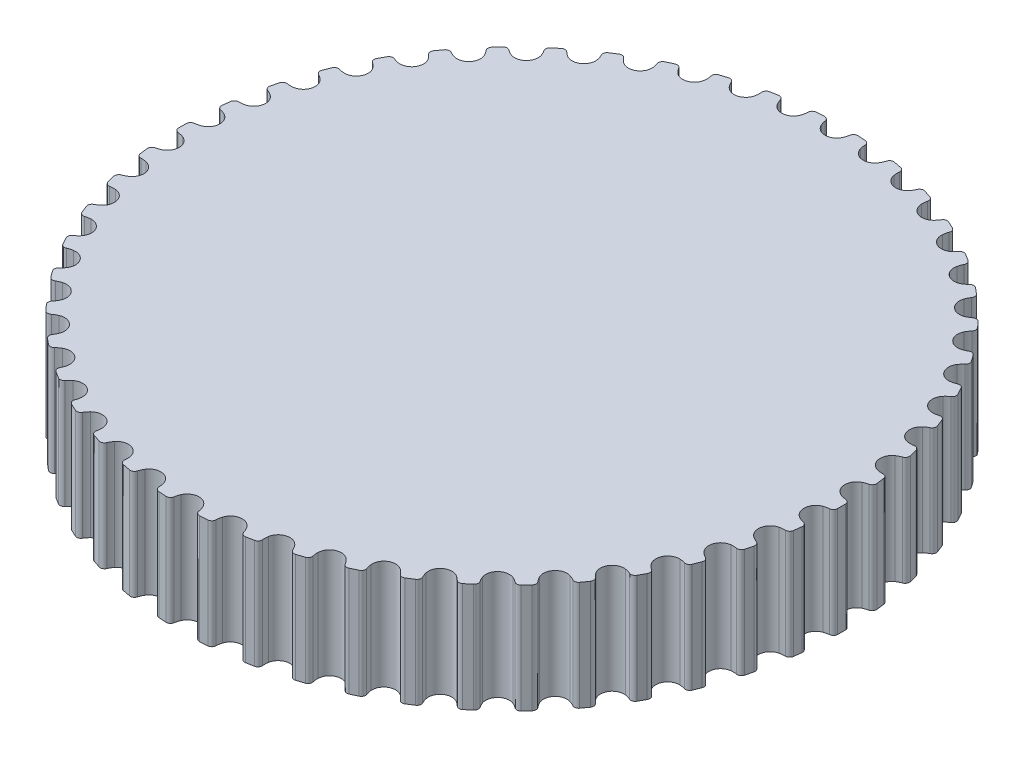
SolidWorks part; units mm, degrees
ref_plane "Front Plane" through (0, 0, 0) normal (0, 0, 1) x (1, 0, 0)
ref_plane "Top Plane" through (0, 0, 0) normal (0, 1, 0) x (1, 0, 0)
ref_plane "Right Plane" through (0, 0, 0) normal (1, 0, 0) x (0, 0, -1)
sketch "Sketch2" plane through (0, 0, 0) normal (0, 1, 0) x (1, 0, 0)
  line L0 (-2.9224, 39.1649) -> (-2.0093, 39.2223)
  line L1 (0, 0) -> (0, 24.0134) construction
  line L2 (-1.9774, 38.7153) -> (0, 38.7122) construction
  line L3 (1.9774, 38.7153) -> (0, 38.7122) construction
  line L4 (0, 0) -> (-2.9254, 23.2185) construction
  line L5 (2.0093, 39.2223) -> (2.9224, 39.1649)
  line L6 (6.9093, 38.6612) -> (7.8081, 38.4898)
  line L7 (11.7003, 37.4904) -> (12.5705, 37.2077)
  line L8 (16.3069, 35.7283) -> (17.1348, 35.3388)
  line L9 (20.6562, 33.4028) -> (21.4288, 32.9126)
  line L10 (24.6798, 30.5505) -> (25.3848, 29.9673)
  line L11 (28.3142, 27.2164) -> (28.9406, 26.5494)
  line L12 (31.5021, 23.4531) -> (32.0399, 22.7129)
  line L13 (34.1931, 19.3199) -> (34.6339, 18.5181)
  line L14 (36.3449, 14.882) -> (36.6818, 14.0313)
  line L15 (37.9236, 10.2094) -> (38.1511, 9.3232)
  line L16 (38.9041, 5.3759) -> (39.0188, 4.4681)
  line L17 (39.2711, 0.4575) -> (39.2711, -0.4575)
  line L18 (39.0188, -4.4681) -> (38.9041, -5.3759)
  line L19 (38.1511, -9.3232) -> (37.9236, -10.2094)
  line L20 (36.6818, -14.0313) -> (36.3449, -14.882)
  line L21 (34.6339, -18.5181) -> (34.1931, -19.3199)
  line L22 (32.0399, -22.7129) -> (31.5021, -23.4531)
  line L23 (28.9406, -26.5494) -> (28.3142, -27.2164)
  line L24 (25.3848, -29.9673) -> (24.6798, -30.5505)
  line L25 (21.4288, -32.9126) -> (20.6562, -33.4028)
  line L26 (17.1348, -35.3388) -> (16.3069, -35.7283)
  line L27 (12.5705, -37.2077) -> (11.7003, -37.4904)
  line L28 (7.8081, -38.4898) -> (6.9093, -38.6612)
  line L29 (2.9224, -39.1649) -> (2.0093, -39.2223)
  line L30 (-2.0093, -39.2223) -> (-2.9224, -39.1649)
  line L31 (-6.9093, -38.6612) -> (-7.8081, -38.4898)
  line L32 (-11.7003, -37.4904) -> (-12.5705, -37.2077)
  line L33 (-16.3069, -35.7283) -> (-17.1348, -35.3388)
  line L34 (-20.6562, -33.4028) -> (-21.4288, -32.9126)
  line L35 (-24.6798, -30.5505) -> (-25.3848, -29.9673)
  line L36 (-28.3142, -27.2164) -> (-28.9406, -26.5494)
  line L37 (-31.5021, -23.4531) -> (-32.0399, -22.7129)
  line L38 (-34.1931, -19.3199) -> (-34.6339, -18.5181)
  line L39 (-36.3449, -14.882) -> (-36.6818, -14.0313)
  line L40 (-37.9236, -10.2094) -> (-38.1511, -9.3232)
  line L41 (-38.9041, -5.3759) -> (-39.0188, -4.4681)
  line L42 (-39.2711, -0.4575) -> (-39.2711, 0.4575)
  line L43 (-39.0188, 4.4681) -> (-38.9041, 5.3759)
  line L44 (-38.1511, 9.3232) -> (-37.9236, 10.2094)
  line L45 (-36.6818, 14.0313) -> (-36.3449, 14.882)
  line L46 (-34.6339, 18.5181) -> (-34.1931, 19.3199)
  line L47 (-32.0399, 22.7129) -> (-31.5021, 23.4531)
  line L48 (-28.9406, 26.5494) -> (-28.3142, 27.2164)
  line L49 (-25.3848, 29.9673) -> (-24.6798, 30.5505)
  line L50 (-21.4288, 32.9126) -> (-20.6562, 33.4028)
  line L51 (-17.1348, 35.3388) -> (-16.3069, 35.7283)
  line L52 (-12.5705, 37.2077) -> (-11.7003, 37.4904)
  line L53 (-7.8081, 38.4898) -> (-6.9093, 38.6612)
  line L54 (0, 0) -> (1.2885, 38.153) construction
  arc A0 (-2.0093, 39.2223) -> (-1.4757, 38.7951) centre (-1.9774, 38.7153) cw
  arc A1 (-1.4757, 38.7951) -> (-1.2885, 38.153) centre (1.1557, 39.2137) ccw
  arc A2 (-1.2885, 38.153) -> (1.2885, 38.153) centre (0, 38.7122) ccw
  arc A3 (1.4757, 38.7951) -> (1.2885, 38.153) centre (-1.1557, 39.2137) cw
  arc A4 (2.0093, 39.2223) -> (1.4757, 38.7951) centre (1.9774, 38.7153) ccw
  arc A5 (0, 38.7122) -> (-4.8393, 38.4085) centre (0, 0) ccw construction
  arc A6 (2.9224, 39.1649) -> (3.3983, 38.6742) centre (2.8905, 38.6579) cw
  arc A7 (3.3983, 38.6742) -> (3.5035, 38.0136) centre (6.0614, 38.7596) ccw
  arc A8 (3.5035, 38.0136) -> (6.0602, 37.6906) centre (4.8519, 38.4069) ccw
  arc A9 (6.3264, 38.3043) -> (6.0602, 37.6906) centre (3.7682, 39.0493) cw
  arc A10 (6.9093, 38.6612) -> (6.3264, 38.3043) centre (6.8141, 38.1622) ccw
  arc A11 (7.8081, 38.4898) -> (8.2186, 37.9433) centre (7.7129, 37.9908) cw
  arc A12 (8.2186, 37.9433) -> (8.2402, 37.2748) centre (10.8714, 37.6943) ccw
  arc A13 (8.2402, 37.2748) -> (10.7363, 36.6339) centre (9.6273, 37.4959) ccw
  arc A14 (11.0773, 37.2093) -> (10.7363, 36.6339) centre (8.6327, 38.2691) cw
  arc A15 (11.7003, 37.4904) -> (11.0773, 37.2093) centre (11.5434, 37.0073) ccw
  arc A16 (12.5705, 37.2077) -> (12.9094, 36.614) centre (12.4136, 36.7245) cw
  arc A17 (12.9094, 36.614) -> (12.847, 35.9481) centre (15.5101, 36.0345) ccw
  arc A18 (12.847, 35.9481) -> (15.2431, 34.9994) centre (14.2509, 35.9937) ccw
  arc A19 (15.6535, 35.5276) -> (15.2431, 34.9994) centre (13.361, 36.8854) cw
  arc A20 (16.3069, 35.7283) -> (15.6535, 35.5276) centre (16.0906, 35.2687) ccw
  arc A21 (17.1348, 35.3388) -> (17.3966, 34.7074) centre (16.9185, 34.8791) cw
  arc A22 (17.3966, 34.7074) -> (17.2512, 34.0544) centre (19.9041, 33.8065) ccw
  arc A23 (17.2512, 34.0544) -> (19.5095, 32.813) centre (18.6497, 33.9237) ccw
  arc A24 (19.9828, 33.2855) -> (19.5095, 32.813) centre (17.8786, 34.92) cw
  arc A25 (20.6562, 33.4028) -> (19.9828, 33.2855) centre (20.384, 32.9739) ccw
  arc A26 (21.4288, 32.9126) -> (21.6094, 32.2533) centre (21.1566, 32.4836) cw
  arc A27 (21.6094, 32.2533) -> (21.3833, 31.6238) centre (23.9842, 31.0453) ccw
  arc A28 (21.3833, 31.6238) -> (23.4682, 30.109) centre (22.7544, 31.3188) ccw
  arc A29 (23.9971, 30.5185) -> (23.4682, 30.109) centre (22.1143, 32.4039) cw
  arc A30 (24.6798, 30.5505) -> (23.9971, 30.5185) centre (24.356, 30.1591) ccw
  arc A31 (25.3848, 29.9673) -> (25.4814, 29.2906) centre (25.061, 29.5759) cw
  arc A32 (25.4814, 29.2906) -> (25.1782, 28.6944) centre (27.6861, 27.7944) ccw
  arc A33 (25.1782, 28.6944) -> (27.0568, 26.9303) centre (26.5003, 28.2199) ccw
  arc A34 (27.6328, 27.2703) -> (27.0568, 26.9303) centre (26.0012, 29.3767) cw
  arc A35 (28.3142, 27.2164) -> (27.6328, 27.2703) centre (27.9439, 26.8687) ccw
  arc A36 (28.9406, 26.5494) -> (28.9515, 25.866) centre (28.5703, 26.2017) cw
  arc A37 (28.9515, 25.866) -> (28.576, 25.3124) centre (30.9514, 24.1053) ccw
  arc A38 (28.576, 25.3124) -> (30.2187, 23.3268) centre (29.8282, 24.6761) ccw
  arc A39 (30.8328, 23.5919) -> (30.2187, 23.3268) centre (29.478, 25.8862) cw
  arc A40 (31.5021, 23.4531) -> (30.8328, 23.5919) centre (31.0911, 23.1545) ccw
  arc A41 (32.0399, 22.7129) -> (31.9651, 22.0334) centre (31.6289, 22.4143) cw
  arc A42 (31.9651, 22.0334) -> (31.5232, 21.5313) centre (33.7285, 20.036) ccw
  arc A43 (31.5232, 21.5313) -> (32.904, 19.3555) centre (32.6858, 20.743) ccw
  arc A44 (33.5465, 19.5415) -> (32.904, 19.3555) centre (32.49, 21.9875) cw
  arc A45 (34.1931, 19.3199) -> (33.5465, 19.5415) centre (33.748, 19.0752) ccw
  arc A46 (34.6339, 18.5181) -> (34.4746, 17.8534) centre (34.1888, 18.2734) cw
  arc A47 (34.4746, 17.8534) -> (33.9732, 17.4106) centre (35.9737, 15.6507) ccw
  arc A48 (33.9732, 17.4106) -> (35.0705, 15.0789) centre (35.0278, 16.4828) ccw
  arc A49 (35.7312, 15.1829) -> (35.0705, 15.0789) centre (34.9896, 17.7421) cw
  arc A50 (36.3449, 14.882) -> (35.7312, 15.1829) centre (35.8726, 14.695) ccw
  arc A51 (36.6818, 14.0313) -> (36.4404, 13.3918) centre (36.2094, 13.8443) cw
  arc A52 (36.4404, 13.3918) -> (35.8875, 13.0154) centre (37.6516, 11.0186) ccw
  arc A53 (35.8875, 13.0154) -> (36.6838, 10.5645) centre (36.8174, 11.9627) ccw
  arc A54 (37.3524, 10.5849) -> (36.6838, 10.5645) centre (36.9373, 13.2168) cw
  arc A55 (37.9236, 10.2094) -> (37.3524, 10.5849) centre (37.4315, 10.0831) ccw
  arc A56 (38.1511, 9.3232) -> (37.8315, 8.719) centre (37.6591, 9.1969) cw
  arc A57 (37.8315, 8.719) -> (37.2357, 8.4148) centre (38.7357, 6.2127) ccw
  arc A58 (37.2357, 8.4148) -> (37.7186, 5.8835) centre (38.0265, 7.2539) ccw
  arc A59 (38.3845, 5.8199) -> (37.7186, 5.8835) centre (38.3026, 8.4831) cw
  arc A60 (38.9041, 5.3759) -> (38.3845, 5.8199) centre (38.4001, 5.3122) ccw
  arc A61 (39.0188, 4.4681) -> (38.6259, 3.9087) centre (38.5148, 4.4044) cw
  arc A62 (38.6259, 3.9087) -> (37.9968, 3.6816) centre (39.2089, 1.3088) ccw
  arc A63 (37.9968, 3.6816) -> (38.1586, 1.1097) centre (38.6358, 2.4308) ccw
  arc A64 (38.8112, 0.9632) -> (38.1586, 1.1097) centre (39.0638, 3.6157) cw
  arc A65 (39.2711, 0.4575) -> (38.8112, 0.9632) centre (38.7631, 0.4575) ccw
  arc A66 (39.2711, -0.4575) -> (38.8112, -0.9632) centre (38.7631, -0.4575) cw
  arc A67 (38.8112, -0.9632) -> (38.1586, -1.1097) centre (39.0638, -3.6157) ccw
  arc A68 (38.1586, -1.1097) -> (37.9968, -3.6816) centre (38.6358, -2.4308) ccw
  arc A69 (38.6259, -3.9087) -> (37.9968, -3.6816) centre (39.2089, -1.3088) cw
  arc A70 (39.0188, -4.4681) -> (38.6259, -3.9087) centre (38.5148, -4.4044) ccw
  arc A71 (38.9041, -5.3759) -> (38.3845, -5.8199) centre (38.4001, -5.3122) cw
  arc A72 (38.3845, -5.8199) -> (37.7186, -5.8835) centre (38.3026, -8.4831) ccw
  arc A73 (37.7186, -5.8835) -> (37.2357, -8.4148) centre (38.0265, -7.2539) ccw
  arc A74 (37.8315, -8.719) -> (37.2357, -8.4148) centre (38.7357, -6.2127) cw
  arc A75 (38.1511, -9.3232) -> (37.8315, -8.719) centre (37.6591, -9.1969) ccw
  arc A76 (37.9236, -10.2094) -> (37.3524, -10.5849) centre (37.4315, -10.0831) cw
  arc A77 (37.3524, -10.5849) -> (36.6838, -10.5645) centre (36.9373, -13.2168) ccw
  arc A78 (36.6838, -10.5645) -> (35.8875, -13.0154) centre (36.8174, -11.9627) ccw
  arc A79 (36.4404, -13.3918) -> (35.8875, -13.0154) centre (37.6516, -11.0186) cw
  arc A80 (36.6818, -14.0313) -> (36.4404, -13.3918) centre (36.2094, -13.8443) ccw
  arc A81 (36.3449, -14.882) -> (35.7312, -15.1829) centre (35.8726, -14.695) cw
  arc A82 (35.7312, -15.1829) -> (35.0705, -15.0789) centre (34.9896, -17.7421) ccw
  arc A83 (35.0705, -15.0789) -> (33.9732, -17.4106) centre (35.0278, -16.4828) ccw
  arc A84 (34.4746, -17.8534) -> (33.9732, -17.4106) centre (35.9737, -15.6507) cw
  arc A85 (34.6339, -18.5181) -> (34.4746, -17.8534) centre (34.1888, -18.2734) ccw
  arc A86 (34.1931, -19.3199) -> (33.5465, -19.5415) centre (33.748, -19.0752) cw
  arc A87 (33.5465, -19.5415) -> (32.904, -19.3555) centre (32.49, -21.9875) ccw
  arc A88 (32.904, -19.3555) -> (31.5232, -21.5313) centre (32.6858, -20.743) ccw
  arc A89 (31.9651, -22.0334) -> (31.5232, -21.5313) centre (33.7285, -20.036) cw
  arc A90 (32.0399, -22.7129) -> (31.9651, -22.0334) centre (31.6289, -22.4143) ccw
  arc A91 (31.5021, -23.4531) -> (30.8328, -23.5919) centre (31.0911, -23.1545) cw
  arc A92 (30.8328, -23.5919) -> (30.2187, -23.3268) centre (29.478, -25.8862) ccw
  arc A93 (30.2187, -23.3268) -> (28.576, -25.3124) centre (29.8282, -24.6761) ccw
  arc A94 (28.9515, -25.866) -> (28.576, -25.3124) centre (30.9514, -24.1053) cw
  arc A95 (28.9406, -26.5494) -> (28.9515, -25.866) centre (28.5703, -26.2017) ccw
  arc A96 (28.3142, -27.2164) -> (27.6328, -27.2703) centre (27.9439, -26.8687) cw
  arc A97 (27.6328, -27.2703) -> (27.0568, -26.9303) centre (26.0012, -29.3767) ccw
  arc A98 (27.0568, -26.9303) -> (25.1782, -28.6944) centre (26.5003, -28.2199) ccw
  arc A99 (25.4814, -29.2906) -> (25.1782, -28.6944) centre (27.6861, -27.7944) cw
  arc A100 (25.3848, -29.9673) -> (25.4814, -29.2906) centre (25.061, -29.5759) ccw
  arc A101 (24.6798, -30.5505) -> (23.9971, -30.5185) centre (24.356, -30.1591) cw
  arc A102 (23.9971, -30.5185) -> (23.4682, -30.109) centre (22.1143, -32.4039) ccw
  arc A103 (23.4682, -30.109) -> (21.3833, -31.6238) centre (22.7544, -31.3188) ccw
  arc A104 (21.6094, -32.2533) -> (21.3833, -31.6238) centre (23.9842, -31.0453) cw
  arc A105 (21.4288, -32.9126) -> (21.6094, -32.2533) centre (21.1566, -32.4836) ccw
  arc A106 (20.6562, -33.4028) -> (19.9828, -33.2855) centre (20.384, -32.9739) cw
  arc A107 (19.9828, -33.2855) -> (19.5095, -32.813) centre (17.8786, -34.92) ccw
  arc A108 (19.5095, -32.813) -> (17.2512, -34.0544) centre (18.6497, -33.9237) ccw
  arc A109 (17.3966, -34.7074) -> (17.2512, -34.0544) centre (19.9041, -33.8065) cw
  arc A110 (17.1348, -35.3388) -> (17.3966, -34.7074) centre (16.9185, -34.8791) ccw
  arc A111 (16.3069, -35.7283) -> (15.6535, -35.5276) centre (16.0906, -35.2687) cw
  arc A112 (15.6535, -35.5276) -> (15.2431, -34.9994) centre (13.361, -36.8854) ccw
  arc A113 (15.2431, -34.9994) -> (12.847, -35.9481) centre (14.2509, -35.9937) ccw
  arc A114 (12.9094, -36.614) -> (12.847, -35.9481) centre (15.5101, -36.0345) cw
  arc A115 (12.5705, -37.2077) -> (12.9094, -36.614) centre (12.4136, -36.7245) ccw
  arc A116 (11.7003, -37.4904) -> (11.0773, -37.2093) centre (11.5434, -37.0073) cw
  arc A117 (11.0773, -37.2093) -> (10.7363, -36.6339) centre (8.6327, -38.2691) ccw
  arc A118 (10.7363, -36.6339) -> (8.2402, -37.2748) centre (9.6273, -37.4959) ccw
  arc A119 (8.2186, -37.9433) -> (8.2402, -37.2748) centre (10.8714, -37.6943) cw
  arc A120 (7.8081, -38.4898) -> (8.2186, -37.9433) centre (7.7129, -37.9908) ccw
  arc A121 (6.9093, -38.6612) -> (6.3264, -38.3043) centre (6.8141, -38.1622) cw
  arc A122 (6.3264, -38.3043) -> (6.0602, -37.6906) centre (3.7682, -39.0493) ccw
  arc A123 (6.0602, -37.6906) -> (3.5035, -38.0136) centre (4.8519, -38.4069) ccw
  arc A124 (3.3983, -38.6742) -> (3.5035, -38.0136) centre (6.0614, -38.7596) cw
  arc A125 (2.9224, -39.1649) -> (3.3983, -38.6742) centre (2.8905, -38.6579) ccw
  arc A126 (2.0093, -39.2223) -> (1.4757, -38.7951) centre (1.9774, -38.7153) cw
  arc A127 (1.4757, -38.7951) -> (1.2885, -38.153) centre (-1.1557, -39.2137) ccw
  arc A128 (1.2885, -38.153) -> (-1.2885, -38.153) centre (0, -38.7122) ccw
  arc A129 (-1.4757, -38.7951) -> (-1.2885, -38.153) centre (1.1557, -39.2137) cw
  arc A130 (-2.0093, -39.2223) -> (-1.4757, -38.7951) centre (-1.9774, -38.7153) ccw
  arc A131 (-2.9224, -39.1649) -> (-3.3983, -38.6742) centre (-2.8905, -38.6579) cw
  arc A132 (-3.3983, -38.6742) -> (-3.5035, -38.0136) centre (-6.0614, -38.7596) ccw
  arc A133 (-3.5035, -38.0136) -> (-6.0602, -37.6906) centre (-4.8519, -38.4069) ccw
  arc A134 (-6.3264, -38.3043) -> (-6.0602, -37.6906) centre (-3.7682, -39.0493) cw
  arc A135 (-6.9093, -38.6612) -> (-6.3264, -38.3043) centre (-6.8141, -38.1622) ccw
  arc A136 (-7.8081, -38.4898) -> (-8.2186, -37.9433) centre (-7.7129, -37.9908) cw
  arc A137 (-8.2186, -37.9433) -> (-8.2402, -37.2748) centre (-10.8714, -37.6943) ccw
  arc A138 (-8.2402, -37.2748) -> (-10.7363, -36.6339) centre (-9.6273, -37.4959) ccw
  arc A139 (-11.0773, -37.2093) -> (-10.7363, -36.6339) centre (-8.6327, -38.2691) cw
  arc A140 (-11.7003, -37.4904) -> (-11.0773, -37.2093) centre (-11.5434, -37.0073) ccw
  arc A141 (-12.5705, -37.2077) -> (-12.9094, -36.614) centre (-12.4136, -36.7245) cw
  arc A142 (-12.9094, -36.614) -> (-12.847, -35.9481) centre (-15.5101, -36.0345) ccw
  arc A143 (-12.847, -35.9481) -> (-15.2431, -34.9994) centre (-14.2509, -35.9937) ccw
  arc A144 (-15.6535, -35.5276) -> (-15.2431, -34.9994) centre (-13.361, -36.8854) cw
  arc A145 (-16.3069, -35.7283) -> (-15.6535, -35.5276) centre (-16.0906, -35.2687) ccw
  arc A146 (-17.1348, -35.3388) -> (-17.3966, -34.7074) centre (-16.9185, -34.8791) cw
  arc A147 (-17.3966, -34.7074) -> (-17.2512, -34.0544) centre (-19.9041, -33.8065) ccw
  arc A148 (-17.2512, -34.0544) -> (-19.5095, -32.813) centre (-18.6497, -33.9237) ccw
  arc A149 (-19.9828, -33.2855) -> (-19.5095, -32.813) centre (-17.8786, -34.92) cw
  arc A150 (-20.6562, -33.4028) -> (-19.9828, -33.2855) centre (-20.384, -32.9739) ccw
  arc A151 (-21.4288, -32.9126) -> (-21.6094, -32.2533) centre (-21.1566, -32.4836) cw
  arc A152 (-21.6094, -32.2533) -> (-21.3833, -31.6238) centre (-23.9842, -31.0453) ccw
  arc A153 (-21.3833, -31.6238) -> (-23.4682, -30.109) centre (-22.7544, -31.3188) ccw
  arc A154 (-23.9971, -30.5185) -> (-23.4682, -30.109) centre (-22.1143, -32.4039) cw
  arc A155 (-24.6798, -30.5505) -> (-23.9971, -30.5185) centre (-24.356, -30.1591) ccw
  arc A156 (-25.3848, -29.9673) -> (-25.4814, -29.2906) centre (-25.061, -29.5759) cw
  arc A157 (-25.4814, -29.2906) -> (-25.1782, -28.6944) centre (-27.6861, -27.7944) ccw
  arc A158 (-25.1782, -28.6944) -> (-27.0568, -26.9303) centre (-26.5003, -28.2199) ccw
  arc A159 (-27.6328, -27.2703) -> (-27.0568, -26.9303) centre (-26.0012, -29.3767) cw
  arc A160 (-28.3142, -27.2164) -> (-27.6328, -27.2703) centre (-27.9439, -26.8687) ccw
  arc A161 (-28.9406, -26.5494) -> (-28.9515, -25.866) centre (-28.5703, -26.2017) cw
  arc A162 (-28.9515, -25.866) -> (-28.576, -25.3124) centre (-30.9514, -24.1053) ccw
  arc A163 (-28.576, -25.3124) -> (-30.2187, -23.3268) centre (-29.8282, -24.6761) ccw
  arc A164 (-30.8328, -23.5919) -> (-30.2187, -23.3268) centre (-29.478, -25.8862) cw
  arc A165 (-31.5021, -23.4531) -> (-30.8328, -23.5919) centre (-31.0911, -23.1545) ccw
  arc A166 (-32.0399, -22.7129) -> (-31.9651, -22.0334) centre (-31.6289, -22.4143) cw
  arc A167 (-31.9651, -22.0334) -> (-31.5232, -21.5313) centre (-33.7285, -20.036) ccw
  arc A168 (-31.5232, -21.5313) -> (-32.904, -19.3555) centre (-32.6858, -20.743) ccw
  arc A169 (-33.5465, -19.5415) -> (-32.904, -19.3555) centre (-32.49, -21.9875) cw
  arc A170 (-34.1931, -19.3199) -> (-33.5465, -19.5415) centre (-33.748, -19.0752) ccw
  arc A171 (-34.6339, -18.5181) -> (-34.4746, -17.8534) centre (-34.1888, -18.2734) cw
  arc A172 (-34.4746, -17.8534) -> (-33.9732, -17.4106) centre (-35.9737, -15.6507) ccw
  arc A173 (-33.9732, -17.4106) -> (-35.0705, -15.0789) centre (-35.0278, -16.4828) ccw
  arc A174 (-35.7312, -15.1829) -> (-35.0705, -15.0789) centre (-34.9896, -17.7421) cw
  arc A175 (-36.3449, -14.882) -> (-35.7312, -15.1829) centre (-35.8726, -14.695) ccw
  arc A176 (-36.6818, -14.0313) -> (-36.4404, -13.3918) centre (-36.2094, -13.8443) cw
  arc A177 (-36.4404, -13.3918) -> (-35.8875, -13.0154) centre (-37.6516, -11.0186) ccw
  arc A178 (-35.8875, -13.0154) -> (-36.6838, -10.5645) centre (-36.8174, -11.9627) ccw
  arc A179 (-37.3524, -10.5849) -> (-36.6838, -10.5645) centre (-36.9373, -13.2168) cw
  arc A180 (-37.9236, -10.2094) -> (-37.3524, -10.5849) centre (-37.4315, -10.0831) ccw
  arc A181 (-38.1511, -9.3232) -> (-37.8315, -8.719) centre (-37.6591, -9.1969) cw
  arc A182 (-37.8315, -8.719) -> (-37.2357, -8.4148) centre (-38.7357, -6.2127) ccw
  arc A183 (-37.2357, -8.4148) -> (-37.7186, -5.8835) centre (-38.0265, -7.2539) ccw
  arc A184 (-38.3845, -5.8199) -> (-37.7186, -5.8835) centre (-38.3026, -8.4831) cw
  arc A185 (-38.9041, -5.3759) -> (-38.3845, -5.8199) centre (-38.4001, -5.3122) ccw
  arc A186 (-39.0188, -4.4681) -> (-38.6259, -3.9087) centre (-38.5148, -4.4044) cw
  arc A187 (-38.6259, -3.9087) -> (-37.9968, -3.6816) centre (-39.2089, -1.3088) ccw
  arc A188 (-37.9968, -3.6816) -> (-38.1586, -1.1097) centre (-38.6358, -2.4308) ccw
  arc A189 (-38.8112, -0.9632) -> (-38.1586, -1.1097) centre (-39.0638, -3.6157) cw
  arc A190 (-39.2711, -0.4575) -> (-38.8112, -0.9632) centre (-38.7631, -0.4575) ccw
  arc A191 (-39.2711, 0.4575) -> (-38.8112, 0.9632) centre (-38.7631, 0.4575) cw
  arc A192 (-38.8112, 0.9632) -> (-38.1586, 1.1097) centre (-39.0638, 3.6157) ccw
  arc A193 (-38.1586, 1.1097) -> (-37.9968, 3.6816) centre (-38.6358, 2.4308) ccw
  arc A194 (-38.6259, 3.9087) -> (-37.9968, 3.6816) centre (-39.2089, 1.3088) cw
  arc A195 (-39.0188, 4.4681) -> (-38.6259, 3.9087) centre (-38.5148, 4.4044) ccw
  arc A196 (-38.9041, 5.3759) -> (-38.3845, 5.8199) centre (-38.4001, 5.3122) cw
  arc A197 (-38.3845, 5.8199) -> (-37.7186, 5.8835) centre (-38.3026, 8.4831) ccw
  arc A198 (-37.7186, 5.8835) -> (-37.2357, 8.4148) centre (-38.0265, 7.2539) ccw
  arc A199 (-37.8315, 8.719) -> (-37.2357, 8.4148) centre (-38.7357, 6.2127) cw
  arc A200 (-38.1511, 9.3232) -> (-37.8315, 8.719) centre (-37.6591, 9.1969) ccw
  arc A201 (-37.9236, 10.2094) -> (-37.3524, 10.5849) centre (-37.4315, 10.0831) cw
  arc A202 (-37.3524, 10.5849) -> (-36.6838, 10.5645) centre (-36.9373, 13.2168) ccw
  arc A203 (-36.6838, 10.5645) -> (-35.8875, 13.0154) centre (-36.8174, 11.9627) ccw
  arc A204 (-36.4404, 13.3918) -> (-35.8875, 13.0154) centre (-37.6516, 11.0186) cw
  arc A205 (-36.6818, 14.0313) -> (-36.4404, 13.3918) centre (-36.2094, 13.8443) ccw
  arc A206 (-36.3449, 14.882) -> (-35.7312, 15.1829) centre (-35.8726, 14.695) cw
  arc A207 (-35.7312, 15.1829) -> (-35.0705, 15.0789) centre (-34.9896, 17.7421) ccw
  arc A208 (-35.0705, 15.0789) -> (-33.9732, 17.4106) centre (-35.0278, 16.4828) ccw
  arc A209 (-34.4746, 17.8534) -> (-33.9732, 17.4106) centre (-35.9737, 15.6507) cw
  arc A210 (-34.6339, 18.5181) -> (-34.4746, 17.8534) centre (-34.1888, 18.2734) ccw
  arc A211 (-34.1931, 19.3199) -> (-33.5465, 19.5415) centre (-33.748, 19.0752) cw
  arc A212 (-33.5465, 19.5415) -> (-32.904, 19.3555) centre (-32.49, 21.9875) ccw
  arc A213 (-32.904, 19.3555) -> (-31.5232, 21.5313) centre (-32.6858, 20.743) ccw
  arc A214 (-31.9651, 22.0334) -> (-31.5232, 21.5313) centre (-33.7285, 20.036) cw
  arc A215 (-32.0399, 22.7129) -> (-31.9651, 22.0334) centre (-31.6289, 22.4143) ccw
  arc A216 (-31.5021, 23.4531) -> (-30.8328, 23.5919) centre (-31.0911, 23.1545) cw
  arc A217 (-30.8328, 23.5919) -> (-30.2187, 23.3268) centre (-29.478, 25.8862) ccw
  arc A218 (-30.2187, 23.3268) -> (-28.576, 25.3124) centre (-29.8282, 24.6761) ccw
  arc A219 (-28.9515, 25.866) -> (-28.576, 25.3124) centre (-30.9514, 24.1053) cw
  arc A220 (-28.9406, 26.5494) -> (-28.9515, 25.866) centre (-28.5703, 26.2017) ccw
  arc A221 (-28.3142, 27.2164) -> (-27.6328, 27.2703) centre (-27.9439, 26.8687) cw
  arc A222 (-27.6328, 27.2703) -> (-27.0568, 26.9303) centre (-26.0012, 29.3767) ccw
  arc A223 (-27.0568, 26.9303) -> (-25.1782, 28.6944) centre (-26.5003, 28.2199) ccw
  arc A224 (-25.4814, 29.2906) -> (-25.1782, 28.6944) centre (-27.6861, 27.7944) cw
  arc A225 (-25.3848, 29.9673) -> (-25.4814, 29.2906) centre (-25.061, 29.5759) ccw
  arc A226 (-24.6798, 30.5505) -> (-23.9971, 30.5185) centre (-24.356, 30.1591) cw
  arc A227 (-23.9971, 30.5185) -> (-23.4682, 30.109) centre (-22.1143, 32.4039) ccw
  arc A228 (-23.4682, 30.109) -> (-21.3833, 31.6238) centre (-22.7544, 31.3188) ccw
  arc A229 (-21.6094, 32.2533) -> (-21.3833, 31.6238) centre (-23.9842, 31.0453) cw
  arc A230 (-21.4288, 32.9126) -> (-21.6094, 32.2533) centre (-21.1566, 32.4836) ccw
  arc A231 (-20.6562, 33.4028) -> (-19.9828, 33.2855) centre (-20.384, 32.9739) cw
  arc A232 (-19.9828, 33.2855) -> (-19.5095, 32.813) centre (-17.8786, 34.92) ccw
  arc A233 (-19.5095, 32.813) -> (-17.2512, 34.0544) centre (-18.6497, 33.9237) ccw
  arc A234 (-17.3966, 34.7074) -> (-17.2512, 34.0544) centre (-19.9041, 33.8065) cw
  arc A235 (-17.1348, 35.3388) -> (-17.3966, 34.7074) centre (-16.9185, 34.8791) ccw
  arc A236 (-16.3069, 35.7283) -> (-15.6535, 35.5276) centre (-16.0906, 35.2687) cw
  arc A237 (-15.6535, 35.5276) -> (-15.2431, 34.9994) centre (-13.361, 36.8854) ccw
  arc A238 (-15.2431, 34.9994) -> (-12.847, 35.9481) centre (-14.2509, 35.9937) ccw
  arc A239 (-12.9094, 36.614) -> (-12.847, 35.9481) centre (-15.5101, 36.0345) cw
  arc A240 (-12.5705, 37.2077) -> (-12.9094, 36.614) centre (-12.4136, 36.7245) ccw
  arc A241 (-11.7003, 37.4904) -> (-11.0773, 37.2093) centre (-11.5434, 37.0073) cw
  arc A242 (-11.0773, 37.2093) -> (-10.7363, 36.6339) centre (-8.6327, 38.2691) ccw
  arc A243 (-10.7363, 36.6339) -> (-8.2402, 37.2748) centre (-9.6273, 37.4959) ccw
  arc A244 (-8.2186, 37.9433) -> (-8.2402, 37.2748) centre (-10.8714, 37.6943) cw
  arc A245 (-7.8081, 38.4898) -> (-8.2186, 37.9433) centre (-7.7129, 37.9908) ccw
  arc A246 (-6.9093, 38.6612) -> (-6.3264, 38.3043) centre (-6.8141, 38.1622) cw
  arc A247 (-6.3264, 38.3043) -> (-6.0602, 37.6906) centre (-3.7682, 39.0493) ccw
  arc A248 (-6.0602, 37.6906) -> (-3.5035, 38.0136) centre (-4.8519, 38.4069) ccw
  arc A249 (-3.3983, 38.6742) -> (-3.5035, 38.0136) centre (-6.0614, 38.7596) cw
  arc A250 (-2.9224, 39.1649) -> (-3.3983, 38.6742) centre (-2.8905, 38.6579) ccw
  point P13 (0, 0)
  point P17 (0, 0)
  point P18 (0, 47.9469)
  point P23 (0, 37.3075)
  point P32 (0, 0)
  point P44 (0, 0)
  point P56 (0, 2.3104)
  point P610 (0, 0)
  dimension "D5" = 1.4046
  dimension "D6" = 2.6645
  dimension "D7" = 0.508
  dimension "D2" = 1.6312
  dimension "D1" = 0.915
  dimension "D3" = 0.6707
  dimension "D4" = 4.852
  dimension "D8" = 50
extrude "Boss-Extrude1" add sketch "Sketch2" along normal blind 13
sketch "Reference circle" plane through (0, 0, 0) normal (0, -1, 0) x (1, 0, 0)
  circle A0 centre (0, 0) radius 30.8397 construction
